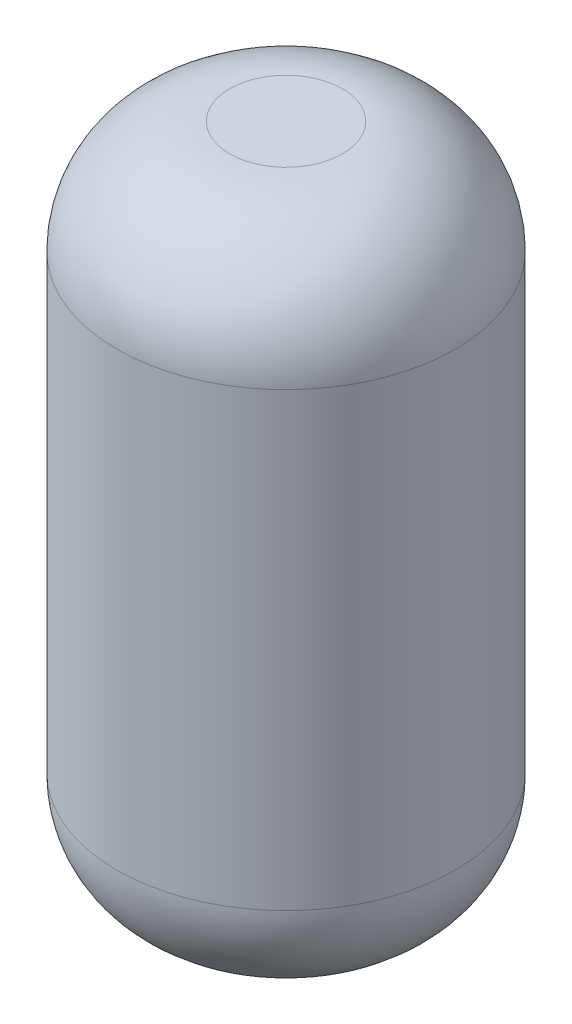
SolidWorks part; units mm, degrees
ref_plane "Plane1" through (0, 0, 0) normal (0, 0, 1) x (1, 0, 0)
ref_plane "Plane2" through (0, 0, 0) normal (0, 1, 0) x (1, 0, 0)
ref_plane "Plane3" through (0, 0, 0) normal (1, 0, 0) x (0, 0, -1)
sketch "Sketch2" plane through (0, 0, 0) normal (0, 1, 0) x (1, 0, 0)
  circle A0 centre (0, 0) radius 9.525
  dimension "D1" = 19.05
extrude "Base-Extrude" add sketch "Sketch2" along normal blind 38.1
fillet "Fillet1" radius 6.35 2 edges at (0, 0, 9.525) (0, 38.1, 9.525)
sketch "Sketch3" plane through (0, 38.1, 0) normal (0, 1, 0) x (-1, 0, 0)
  point P0 (0, 0)
ref_point "Point1"
